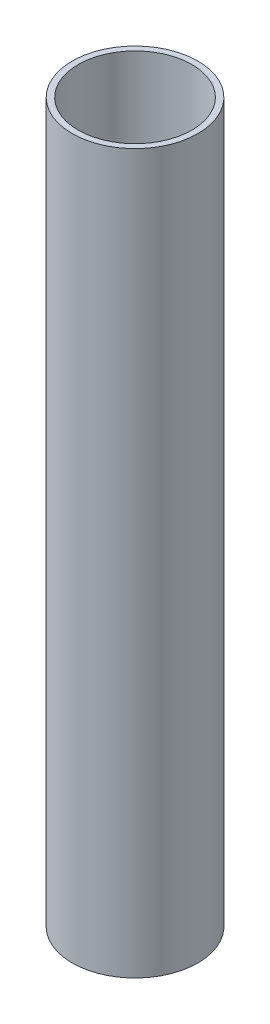
SolidWorks part; units mm, degrees
ref_plane "Front Plane" through (0, 0, 0) normal (0, 0, 1) x (1, 0, 0)
ref_plane "Top Plane" through (0, 0, 0) normal (0, 1, 0) x (1, 0, 0)
ref_plane "Right Plane" through (0, 0, 0) normal (1, 0, 0) x (0, 0, -1)
sketch "Sketch1" plane through (0, 0, 0) normal (0, 1, 0) x (1, 0, 0)
  circle A0 centre (0, 0) radius 19
extrude "Extrude-Thin1" add sketch "Sketch1" along normal blind 240 thin
